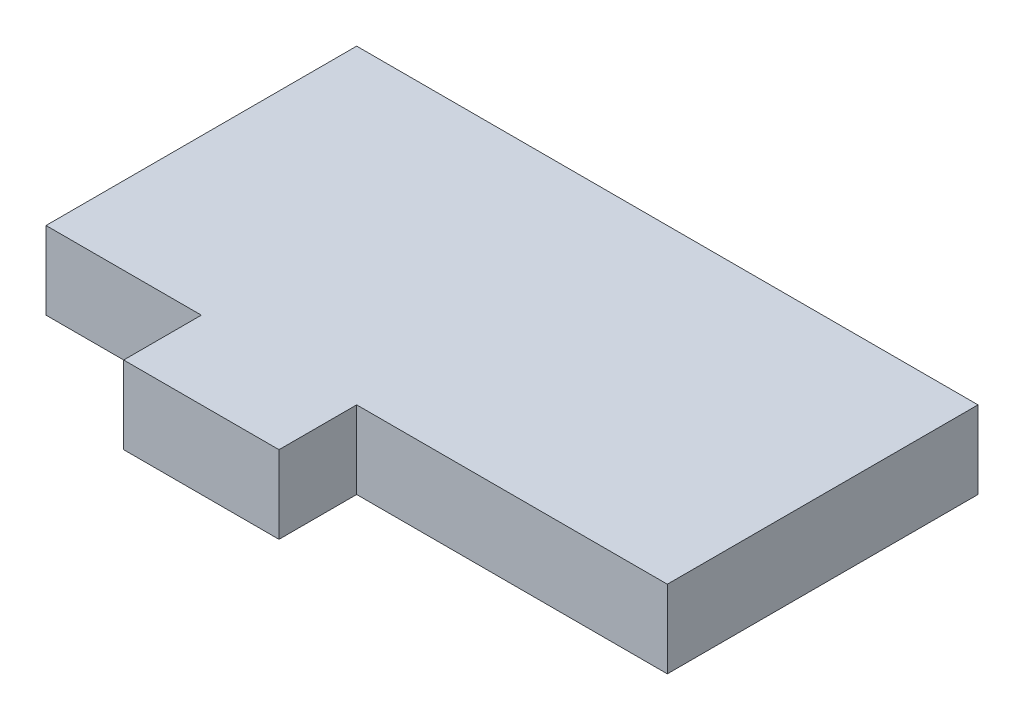
SolidWorks part; units mm, degrees
ref_plane "Front Plane" through (0, 0, 0) normal (0, 0, 1) x (1, 0, 0)
ref_plane "Top Plane" through (0, 0, 0) normal (0, 1, 0) x (1, 0, 0)
ref_plane "Right Plane" through (0, 0, 0) normal (1, 0, 0) x (0, 0, -1)
sketch "Sketch1" plane through (0, 0, 0) normal (0, 1, 0) x (1, 0, 0)
  line L1 (0, 0) -> (50.8, 0)
  line L2 (0, 0) -> (0, 25.4)
  line L3 (0, 25.4) -> (50.8, 25.4)
  line L4 (50.8, 0) -> (50.8, 25.4)
  line L5 (12.7, 0) -> (25.4, 0)
  line L6 (12.7, 0) -> (12.7, -6.35)
  line L7 (12.7, -6.35) -> (25.4, -6.35)
  line L8 (25.4, 0) -> (25.4, -6.35)
  dimension "D1" = 25.4
  dimension "D2" = 50.8
  dimension "D3" = 12.7
  dimension "D4" = 12.7
  dimension "D5" = 6.35
extrude "Boss-Extrude1" add sketch "Sketch1" along normal blind 6.35 contours L8 L1 L6 L7 | L1 L4 L3 L2
